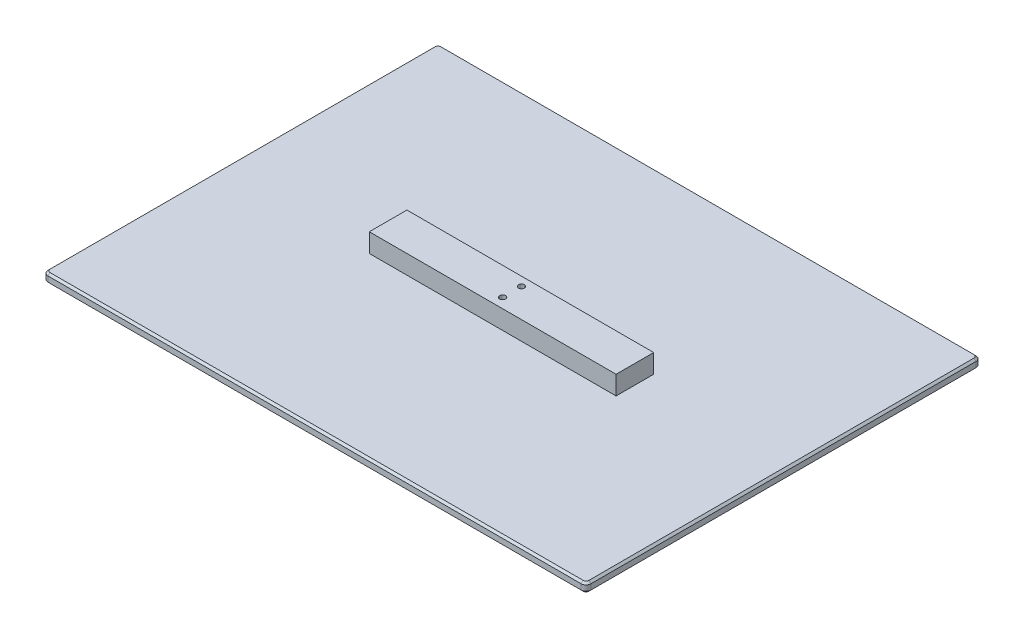
SolidWorks part; units mm, degrees
material "6061-T6 (SS)"
ref_plane "Front Plane" through (0, 0, 0) normal (0, 0, 1) x (1, 0, 0)
ref_plane "Top Plane" through (0, 0, 0) normal (0, 1, 0) x (1, 0, 0)
ref_plane "Right Plane" through (0, 0, 0) normal (1, 0, 0) x (0, 0, -1)
sketch "Sketch1" plane through (0, 0, 0) normal (0, 1, 0) x (1, 0, 0)
  line L1 (-275, 200) -> (275, 200)
  line L2 (-275, 200) -> (-275, -200)
  line L3 (-275, -200) -> (275, -200)
  line L4 (275, 200) -> (275, -200)
  line L5 (-275, 200) -> (275, -200) construction
  line L6 (-275, -200) -> (275, 200) construction
  point P0 (0, 0)
  dimension "D1" = 550
  dimension "D2" = 400
extrude "Boss-Extrude1" add sketch "Sketch1" along normal blind 9.525
sketch "Sketch2" plane through (0, 9.525, 0) normal (0, 1, 0) x (1, 0, 0)
  line L0 (0, 200) -> (0, -200) construction
  line L1 (275, 200) -> (-275, 200) construction
  line L2 (-275, -200) -> (275, -200) construction
  line L3 (-275, 0) -> (275, 0) construction
  line L4 (-275, 200) -> (-275, -200) construction
  line L5 (275, -200) -> (275, 200) construction
  circle A0 centre (0, 9.55) radius 3
  circle A1 centre (0, -9.55) radius 3
  circle A2 centre (-30, 0) radius 3 construction
  circle A3 centre (30, 0) radius 3 construction
  dimension "D1" = 6
  dimension "D4" = 6
  dimension "D5" = 60
  dimension "D2" = 19.1
  dimension "D3" = 9.55
  dimension "D6" = 30
fillet "Fillet1" radius 5 4 edges at (-275, 4.7625, -200) (275, 4.7625, -200) (275, 4.7625, 200) (-275, 4.7625, 200)
chamfer "Chamfer1" distance 2 angle 45 8 edges at (0, 9.525, -200) (-273.5355, 9.525, -198.5355) (273.5355, 9.525, -198.5355) (-275, 9.525, 0) (275, 9.525, 0) (-273.5355, 9.525, 198.5355) (273.5355, 9.525, 198.5355) (0, 9.525, 200)
chamfer "Chamfer2" distance 2 angle 45 8 edges at (0, 0, -200) (-273.5355, 0, -198.5355) (273.5355, 0, -198.5355) (-275, 0, 0) (275, 0, 0) (-273.5355, 0, 198.5355) (273.5355, 0, 198.5355) (0, 0, 200)
sketch "Sketch4" plane through (0, 9.525, 0) normal (0, 1, 0) x (1, 0, 0)
  line L0 (-273, 0) -> (273, 0) construction
  line L5 (-125, 18.55) -> (125, -19.55) construction
  line L6 (125, 18.55) -> (-125, -19.55) construction
  line L7 (0, 198) -> (0, -198) construction
  line L8 (270, 198) -> (-270, 198) construction
  line L9 (-270, -198) -> (270, -198) construction
  line L10 (-273, 195) -> (-273, -195) construction
  line L16 (-125, 18.55) -> (125, 18.55)
  line L21 (-125, 18.55) -> (-125, -19.55)
  line L22 (-125, -19.55) -> (125, -19.55)
  line L23 (273, -195) -> (273, 195) construction
  line L28 (125, 18.55) -> (125, -19.55)
  circle A0 centre (0, -9.55) radius 3 construction
  circle A1 centre (0, 9.55) radius 3 construction
  point P0 (0, -0.5)
  dimension "D3" = 6
  dimension "D1" = 250
  dimension "D2" = 38.1
  dimension "D4" = 10
  dimension "D8" = 19.1
  dimension "D9" = 9.55
extrude "Boss-Extrude3" add sketch "Sketch4" along normal blind 19.05
extrude "Cut-Extrude1" cut sketch "Sketch2" along normal through all
